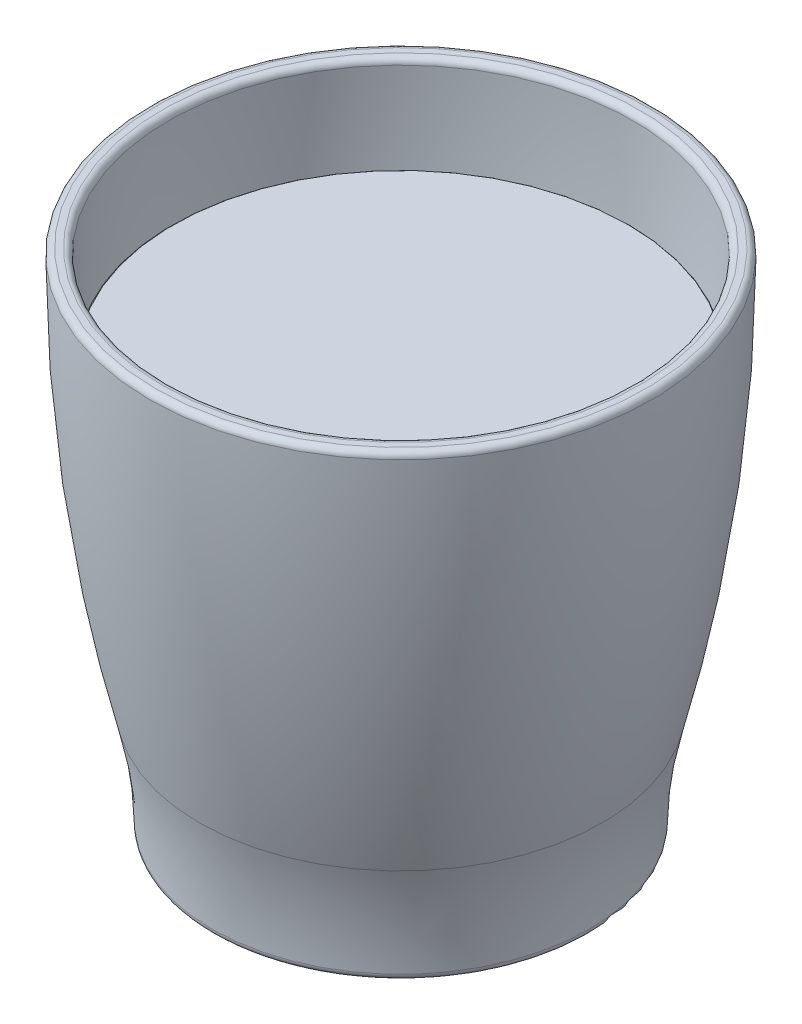
SolidWorks part; units mm, degrees
ref_plane "Front Plane" through (0, 0, 0) normal (0, 0, 1) x (1, 0, 0)
ref_plane "Top Plane" through (0, 0, 0) normal (0, 1, 0) x (1, 0, 0)
ref_plane "Right Plane" through (0, 0, 0) normal (1, 0, 0) x (0, 0, -1)
sketch "Sketch1" plane through (0, 0, 0) normal (0, 0, 1) x (1, 0, 0)
  line L0 (0, 0) -> (0, 80) construction
  line L1 (-40, 80) -> (-40, -19.9946) construction
  line L2 (-30.012, 0) -> (-24.1413, 0)
  line L3 (-16.2754, 2.8761) -> (0, 2.8761)
  line L4 (-40, 80) -> (-37, 80)
  line L5 (-16.793, 7.8761) -> (0, 7.8761)
  line L6 (0, 7.8761) -> (0, 2.8761)
  arc A0 (-40, 80) -> (-32.0978, 16.7069) centre (217.4271, 80) ccw
  arc A1 (-32.0978, 16.7069) -> (-30.012, 0) centre (-97.9626, 0) cw
  arc A2 (-24.1413, 0) -> (-16.2754, 2.8761) centre (-9.7121, -27.268) cw
  arc A3 (-37, 80) -> (-29.1899, 17.4445) centre (217.4271, 80) ccw
  arc A4 (-29.1899, 17.4445) -> (-28.7171, 15.4614) centre (-97.9626, 0) cw
  arc A5 (-16.941, 7.846) -> (-16.793, 7.8761) centre (-9.7121, -27.268) cw
  arc A6 (-29.1899, 17.4445) -> (-27.012, 0) centre (-97.9626, 0) cw construction
  arc A7 (-26.4799, 4.4194) -> (-16.793, 7.8761) centre (-9.7121, -27.268) cw construction
  arc A8 (-28.7171, 15.4614) -> (-16.941, 7.846) centre (-18.9575, 17.6406) ccw
  dimension "D4" = 10
  dimension "D1" = 80
  dimension "D5" = 40
  dimension "D2" = 3
  dimension "D3" = 5
revolve "Revolve1" add sketch "Sketch1" angle 360 about L6
fillet "Fillet1" radius 1 4 edges at (0, 0, 30.012) (0, 0, 24.1413) (0, 80, 37) (0, 80, 40)
sketch "Sketch2" plane through (0, 0, 0) normal (0, 0, 1) x (1, 0, 0)
  line L1 (-36.3571, 65) -> (0, 65)
  line L2 (-16.8129, 8.0761) -> (0, 8.0761)
  line L3 (-16.8129, 8.0761) -> (0, 8.0761)
  line L4 (0, 0) -> (0, 80) construction
  line L5 (0, 65) -> (0, 8.0761)
  line L6 (-40, 80) -> (-37, 80) construction
  arc A18 (-16.8129, 8.0761) -> (-16.9814, 8.0419) centre (-9.7121, -27.268) ccw
  arc A19 (-28.5219, 15.505) -> (-16.9814, 8.0419) centre (-18.9575, 17.6406) ccw
  arc A20 (-28.5219, 15.505) -> (-28.9961, 17.4937) centre (-97.9626, 0) ccw
  arc A21 (-36.8, 80) -> (-28.9961, 17.4937) centre (217.4271, 80) ccw
  arc A22 (-16.8129, 8.0761) -> (-16.9814, 8.0419) centre (-9.7121, -27.268) ccw
  arc A23 (-28.5219, 15.505) -> (-16.9814, 8.0419) centre (-18.9575, 17.6406) ccw
  arc A24 (-28.5219, 15.505) -> (-28.9961, 17.4937) centre (-97.9626, 0) ccw
  arc A25 (-36.3571, 65) -> (-28.9961, 17.4937) centre (217.4271, 80) ccw
  dimension "D2" = 15
  dimension "D1" = 0.2
revolve "Revolve2" add sketch "Sketch2" angle 360 about L0
fillet "Fillet2" radius 0.1 1 edges at (0, 65, -36.3571)
